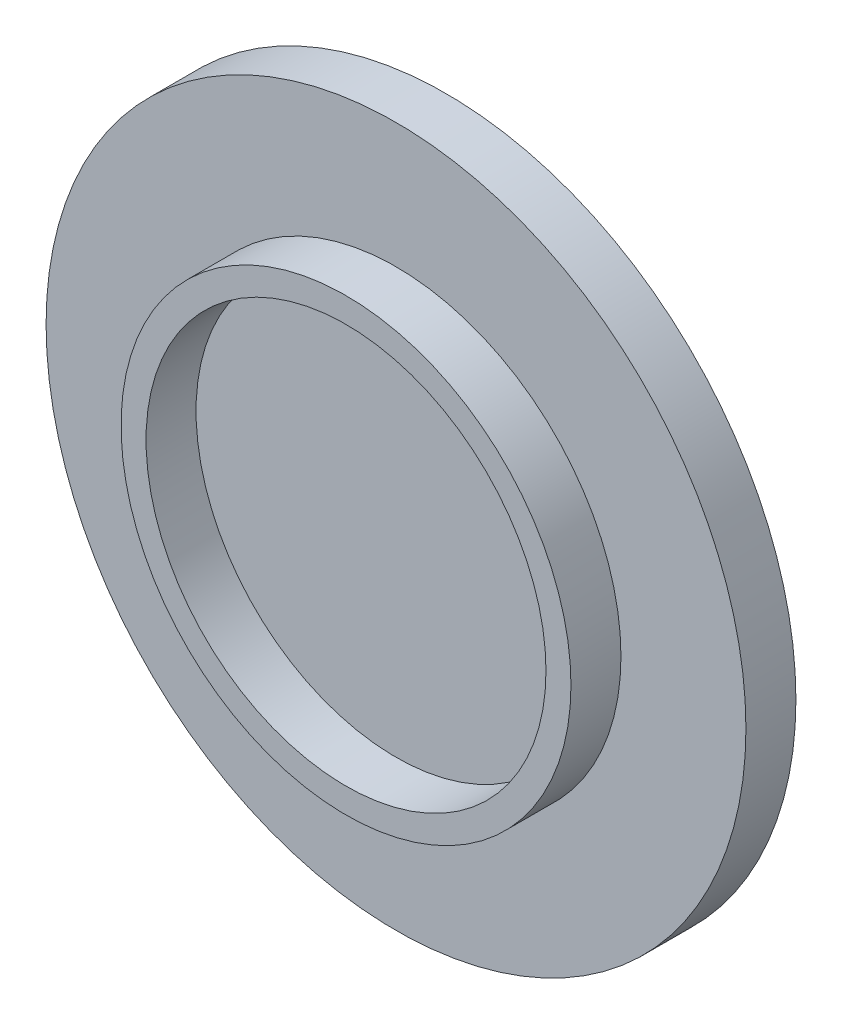
SolidWorks part; units mm, degrees
ref_plane "Płaszczyzna przednia" through (0, 0, 0) normal (0, 0, 1) x (1, 0, 0)
ref_plane "Płaszczyzna górna" through (0, 0, 0) normal (0, 1, 0) x (1, 0, 0)
ref_plane "Płaszczyzna prawa" through (0, 0, 0) normal (1, 0, 0) x (0, 0, -1)
sketch "Szkic1" plane through (0, 0, 0) normal (0, 0, 1) x (1, 0, 0)
  circle A0 centre (0, 0) radius 70
  dimension "D1" = 140
extrude "Dodanie-wyciągnięcie1" add sketch "Szkic1" along normal blind 10
sketch "Szkic2" plane through (0, 0, 10) normal (0, 0, 1) x (1, 0, 0)
  circle A0 centre (0, 0) radius 45
  dimension "D1" = 90
extrude "Dodanie-wyciągnięcie2" add sketch "Szkic2" along normal blind 10
sketch "Szkic3" plane through (0, 0, 20) normal (0, 0, 1) x (1, 0, 0)
  circle A0 centre (0, 0) radius 40
  dimension "D1" = 80
extrude "Wytnij-wyciągnięcie1" cut sketch "Szkic3" against normal blind 10
